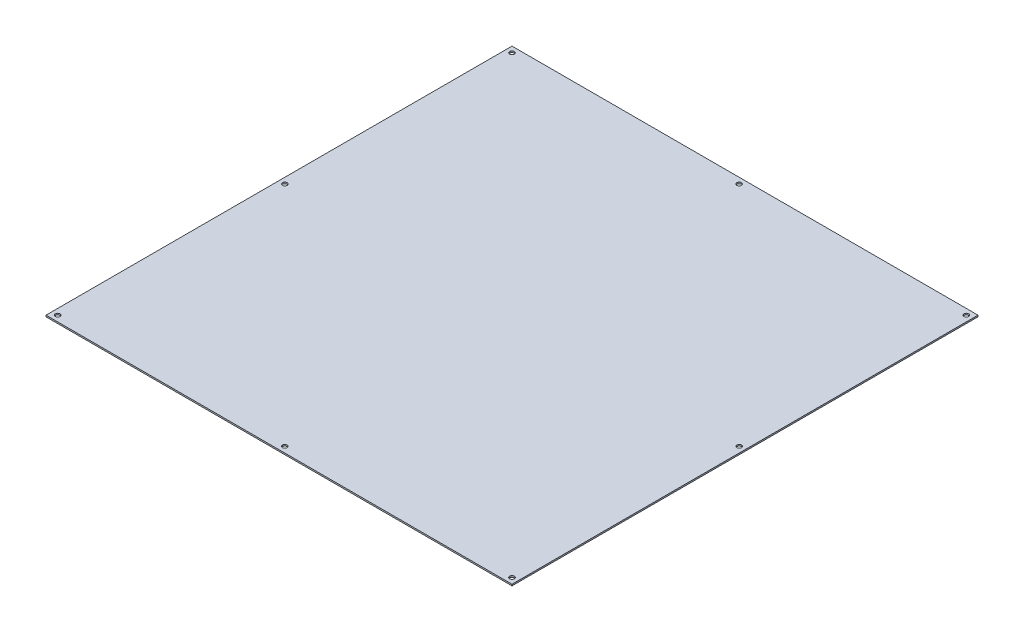
SolidWorks part; units mm, degrees
ref_plane "Front Plane" through (0, 0, 0) normal (0, 0, 1) x (1, 0, 0)
ref_plane "Top Plane" through (0, 0, 0) normal (0, 1, 0) x (1, 0, 0)
ref_plane "Right Plane" through (0, 0, 0) normal (1, 0, 0) x (0, 0, -1)
sketch "main_plate" plane through (0, 0, 0) normal (0, 1, 0) x (1, 0, 0)
  line L1 (-160, 160) -> (160, 160)
  line L2 (-160, 160) -> (-160, -160)
  line L3 (-160, -160) -> (160, -160)
  line L4 (160, 160) -> (160, -160)
  line L5 (-160, 160) -> (160, -160) construction
  line L6 (-160, -160) -> (160, 160) construction
  point P0 (0, 0)
  dimension "D1" = 320
  dimension "D2" = 320
extrude "Boss-Extrude1" add sketch "main_plate" along normal blind 1.016
sketch "main_holes" plane through (0, 1.016, 0) normal (0, 1, 0) x (1, 0, 0)
  line L0 (-160, 160) -> (-160, -160) construction
  line L1 (160, 160) -> (-160, 160) construction
  circle A0 centre (-156, 156) radius 1.6
  circle A24 centre (0, 156) radius 1.6
  circle A34 centre (156, 156) radius 1.6
  circle A35 centre (-156, 0) radius 1.6
  circle A37 centre (156, 0) radius 1.6
  circle A38 centre (-156, -156) radius 1.6
  circle A39 centre (0, -156) radius 1.6
  circle A40 centre (156, -156) radius 1.6
  circle A41 centre (0, 0) radius 1.6 [skipped]
  dimension "D3" = 3.2
  dimension "D1" = 4
  dimension "D2" = 4
  dimension "D4" = 156
  dimension "D5" = 156
  dimension "D6" = 3
extrude "Cut-Extrude1" cut sketch "main_holes" against normal through all
